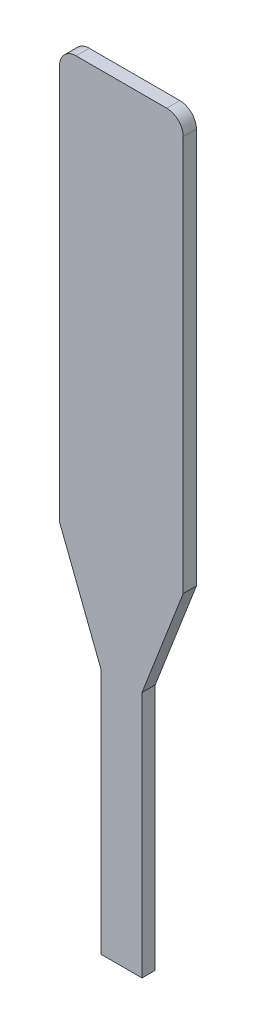
SolidWorks part; units mm, degrees
material "Pure Gold"
ref_plane "Front Plane" through (0, 0, 0) normal (0, 0, 1) x (1, 0, 0)
ref_plane "Top Plane" through (0, 0, 0) normal (0, 1, 0) x (1, 0, 0)
ref_plane "Right Plane" through (0, 0, 0) normal (1, 0, 0) x (0, 0, -1)
sketch "Sketch1" plane through (0, 0, 0) normal (0, 0, 1) x (1, 0, 0)
  line L0 (-49.1053, -44.1202) -> (-49.1053, -54.2802) construction
  line L1 (-49.1053, -47.9302) -> (-47.2003, -47.9302)
  line L2 (-49.1053, -47.9302) -> (-49.1053, -54.2802)
  line L3 (-47.2003, -54.2802) -> (-47.2003, -47.9302)
  line L4 (-47.2003, -54.2802) -> (-47.2003, 17.6018) construction
  line L5 (-48.1528, -47.9302) -> (-48.1528, -59.7278) construction
  line L7 (-48.4703, -59.7278) -> (-47.8353, -59.7278)
  line L8 (-48.4703, -59.7278) -> (-48.4703, -55.9178)
  line L10 (-47.8353, -59.7278) -> (-47.8353, -55.9178)
  line L12 (-49.1053, -54.2802) -> (-47.2003, -54.2802) construction
  line L13 (-47.8353, -55.9178) -> (-47.2003, -54.2802)
  line L14 (-48.4703, -55.9178) -> (-49.1053, -54.2802)
  dimension "D1" = 0.635
  dimension "D2" = 0.3175
  dimension "D3" = 6.35
  dimension "D4" = 3.81
extrude "Boss-Extrude1" add sketch "Sketch1" along normal blind 0.2032
fillet "Fillet2" radius 0.254 2 edges at (-49.1053, -47.9302, 0.1016) (-47.2003, -47.9302, 0.1016)
